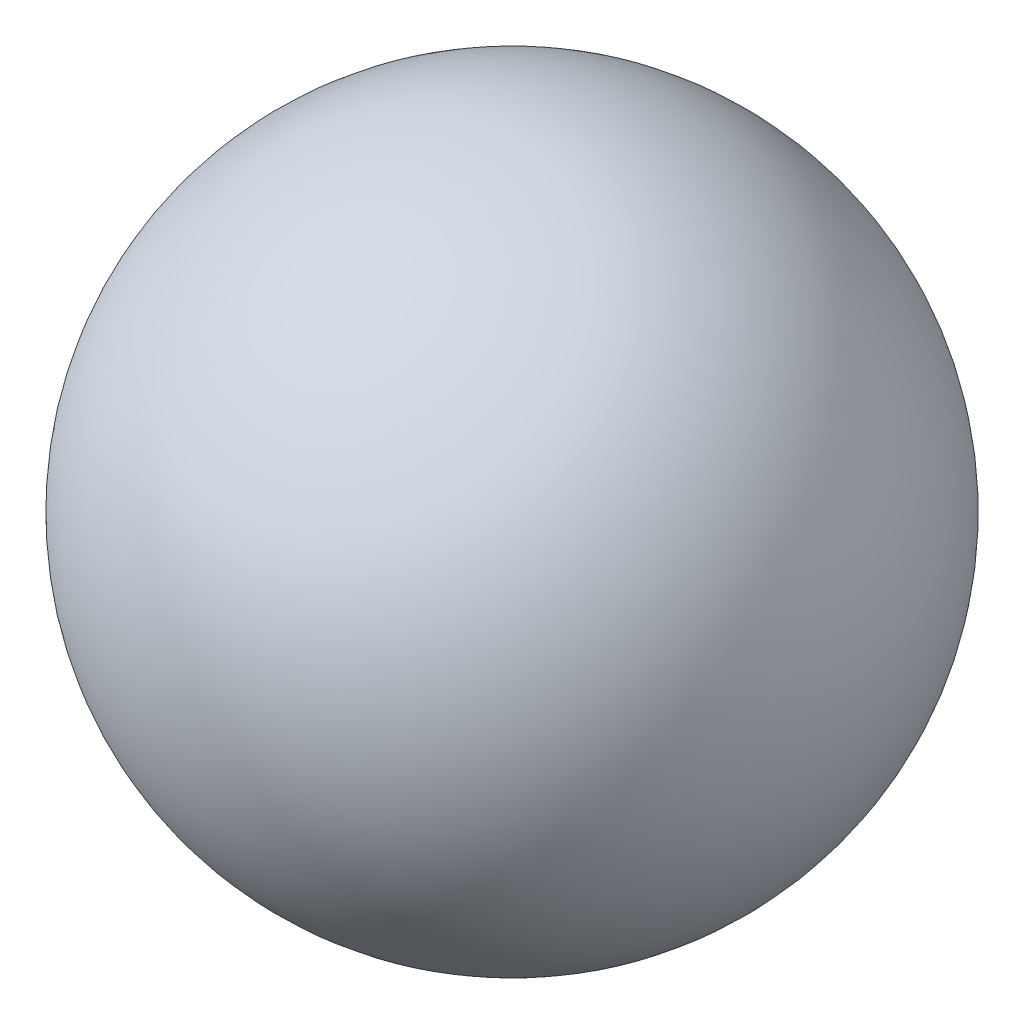
SolidWorks part; units mm, degrees
material "Silicon"
ref_plane "Front Plane" through (0, 0, 0) normal (0, 0, 1) x (1, 0, 0)
ref_plane "Top Plane" through (0, 0, 0) normal (0, 1, 0) x (1, 0, 0)
ref_plane "Right Plane" through (0, 0, 0) normal (1, 0, 0) x (0, 0, -1)
sketch "Sketch1" plane through (0, 0, 0) normal (0, 0, 1) x (1, 0, 0)
  line L0 (0, 6.35) -> (0, -6.35) construction
  line L1 (0, 6.35) -> (0, -6.35)
  arc A0 (0, -6.35) -> (0, 6.35) centre (0, 0) ccw
  dimension "D1" = 12.7
revolve "Revolve2" add sketch "Sketch1" angle 360 about L0
